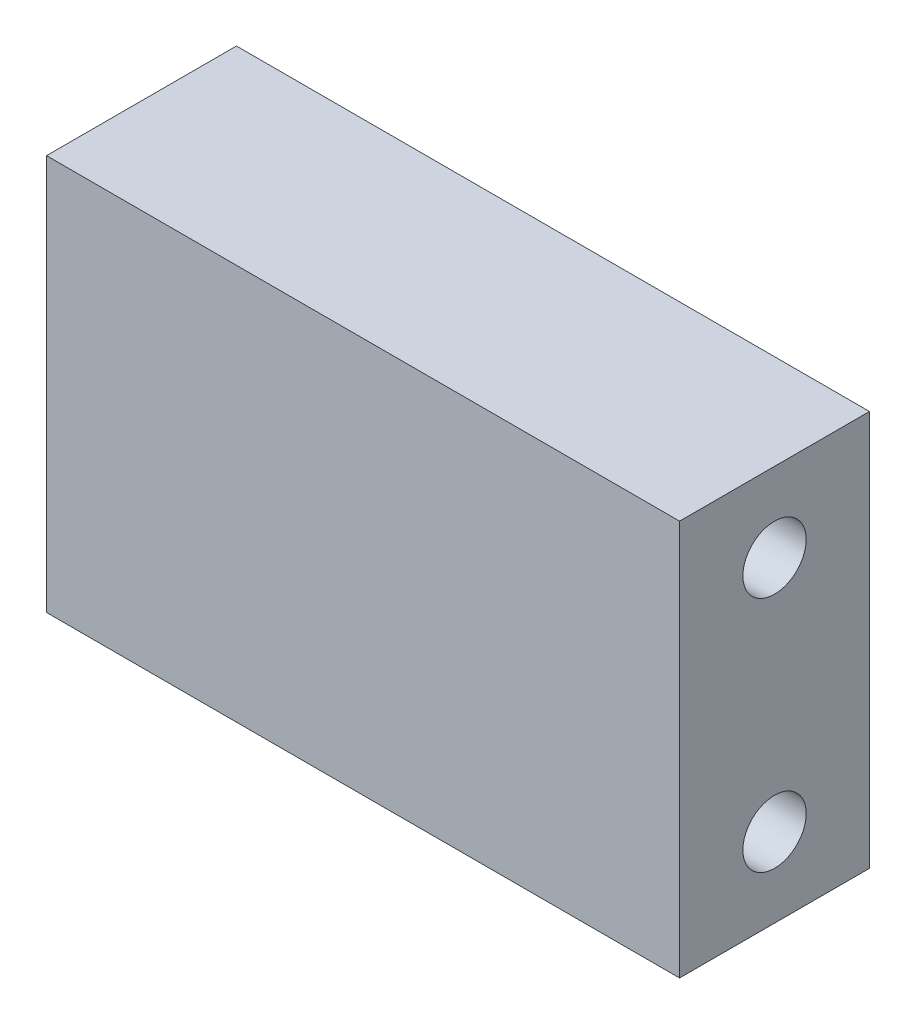
SolidWorks part; units mm, degrees
material "Plastique personnalisé"
ref_plane "Plan de face" through (0, 0, 0) normal (0, 0, 1) x (1, 0, 0)
ref_plane "Plan de dessus" through (0, 0, 0) normal (0, 1, 0) x (1, 0, 0)
ref_plane "Plan de droite" through (0, 0, 0) normal (1, 0, 0) x (0, 0, -1)
sketch "Esquisse1" plane through (0, 0, 0) normal (0, 0, 1) x (1, 0, 0)
  line L1 (0, 0) -> (40, 0)
  line L2 (0, 0) -> (0, 25)
  line L3 (0, 25) -> (40, 25)
  line L4 (40, 0) -> (40, 25)
  dimension "D1" = 40
  dimension "D2" = 25
extrude "Boss.-Extru.1" add sketch "Esquisse1" along normal blind 12
hole_wizard "Diamètre du perçage Ø4.0 (4)1" positions "Esquisse2" profile "Esquisse3" hole size "Ø4.0" standard "Ansi Metric" end condition up to next
sketch "Esquisse2" plane through (40, 0, 0) normal (1, 0, 0) x (0, 0, -1)
  line L0 (-6, 20) -> (-6, 5) construction
  line L2 (-12, 25) -> (0, 25) construction
  line L3 (0, 0) -> (0, 25) construction
  point P0 (-6, 20)
  point P2 (-6, 5)
  dimension "D1" = 15
  dimension "D2" = 5
  dimension "D3" = 6
sketch "Esquisse3" plane through (40, 20, 6) normal (0, 1, 0) x (0, 0, -1)
  line L0 (0, 0) -> (0, 40)
  line L1 (0, 40) -> (2, 40)
  line L2 (2, 40) -> (2, 0)
  line L5 (2, 0) -> (0, 0)
  line L11 (0, -6.35) -> (0, 107.95) construction
  dimension "Diamètre du perçage jusqu'au prochain" = 4
  dimension "Profondeur du perçage jusqu'au prochain" = 40
